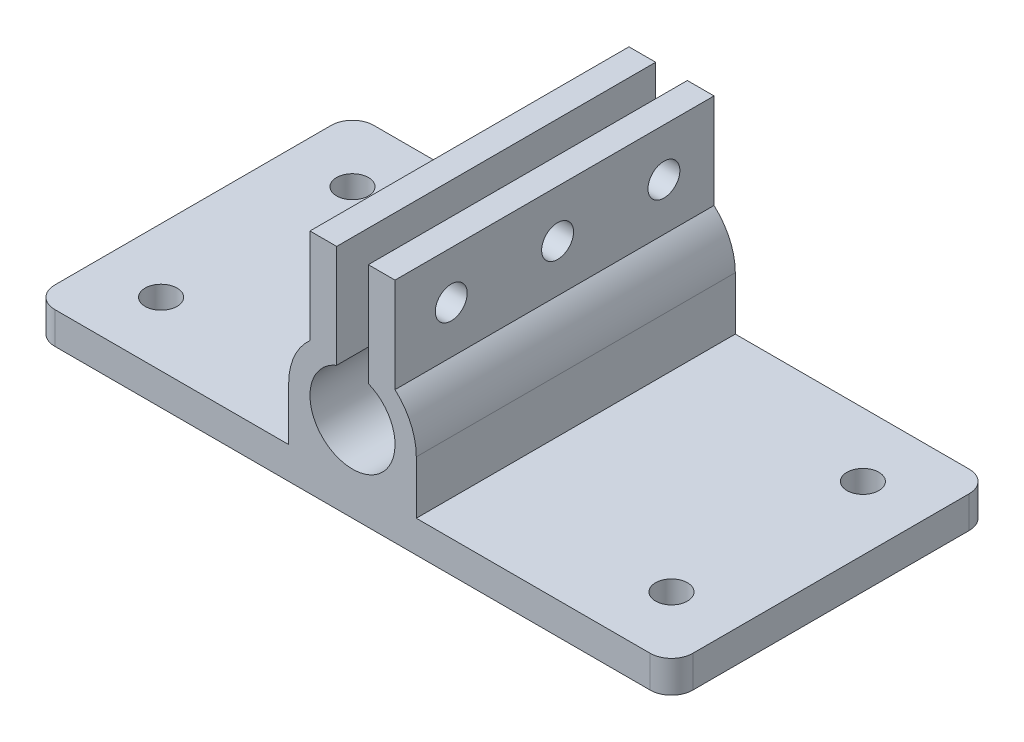
SolidWorks part; units mm, degrees
ref_plane "前视基准面" through (0, 0, 0) normal (0, 0, 1) x (1, 0, 0)
ref_plane "上视基准面" through (0, 0, 0) normal (0, 1, 0) x (1, 0, 0)
ref_plane "右视基准面" through (0, 0, 0) normal (1, 0, 0) x (0, 0, -1)
sketch "草图1" plane through (0, 0, 0) normal (0, 1, 0) x (1, 0, 0)
  line L1 (30, 15) -> (-30, 15)
  line L2 (30, 15) -> (30, -15)
  line L3 (30, -15) -> (-30, -15)
  line L4 (-30, 15) -> (-30, -15)
  line L5 (30, 15) -> (-30, -15) construction
  line L6 (30, -15) -> (-30, 15) construction
  point P0 (0, 0)
extrude "凸台-拉伸1" add sketch "草图1" along normal blind 3
sketch "草图2" plane through (0, 3, 0) normal (0, 1, 0) x (1, 0, 0)
  line L0 (-30, -9) -> (-24, -9) construction
  line L1 (-30, 15) -> (-30, -15) construction
  line L2 (-24, -9) -> (-24, -15) construction
  line L3 (-30, -15) -> (30, -15) construction
  circle A0 centre (-24, -9) radius 1.5
extrude "切除-拉伸1" cut sketch "草图2" against normal blind 3
mirror "镜向1" about plane through (0, 0, 0) normal (0, 0, 1) of "切除-拉伸1"
mirror "镜向2" about plane through (0, 0, 0) normal (1, 0, 0) of "镜向1", "切除-拉伸1"
fillet "圆角2" radius 2 4 edges at (-30, 1.5, -15) (30, 1.5, -15) (30, 1.5, 15) (-30, 1.5, 15)
sketch "草图5" plane through (0, 0, 15) normal (0, 0, 1) x (1, 0, 0)
  line L1 (-28, 3) -> (28, 3) construction
  circle A0 centre (0, 8) radius 6
  dimension "D1" = 5
extrude "凸台-拉伸2" add sketch "草图5" against normal up to surface (30 mm away) up to face at (0, 1.5, -15)
sketch "草图6" plane through (0, 0, 15) normal (0, 0, 1) x (1, 0, 0)
  line L0 (6, 8) -> (6, 3)
  line L1 (3.3166, 3) -> (28, 3) construction
  line L2 (6, 3) -> (-6, 3)
  line L3 (-28, 3) -> (-3.3166, 3) construction
  line L4 (-6, 3) -> (-6, 8)
  line L5 (-6, 8) -> (6, 8)
  arc A0 (3.3166, 3) -> (-3.3166, 3) centre (0, 8) ccw construction
extrude "凸台-拉伸3" add sketch "草图6" against normal up to surface (30 mm away) up to face at (0, 3.8333, -15)
sketch "草图7" plane through (0, 0, 15) normal (0, 0, 1) x (1, 0, 0)
  circle A0 centre (0, 8) radius 4
extrude "切除-拉伸4" cut sketch "草图7" against normal through all
sketch "草图8" plane through (0, 0, 15) normal (0, 0, 1) x (1, 0, 0)
  line L0 (0, 8) -> (0, 22.1886) construction
  line L2 (-4, 21.396) -> (4, 21.396)
  line L3 (-4, 21.396) -> (-4, 12.2415)
  line L4 (-4, 12.2415) -> (4, 12.2415)
  line L5 (4, 21.396) -> (4, 12.2415)
  line L6 (-4, 21.396) -> (4, 12.2415) construction
  line L7 (-4, 12.2415) -> (4, 21.396) construction
  point P4 (0, 16.8188)
  point P9 (0, 16.8188)
extrude "凸台-拉伸4" add sketch "草图8" against normal up to surface (30 mm away) up to face at (4, 8, -15)
sketch "草图9" plane through (0, 0, 15) normal (0, 0, 1) x (1, 0, 0)
  line L1 (-1.4884, 22.8266) -> (1.4884, 22.8266)
  line L2 (-1.4884, 22.8266) -> (-1.4884, 9.9673)
  line L3 (-1.4884, 9.9673) -> (1.4884, 9.9673)
  line L4 (1.4884, 22.8266) -> (1.4884, 9.9673)
  line L5 (-1.4884, 22.8266) -> (1.4884, 9.9673) construction
  line L6 (-1.4884, 9.9673) -> (1.4884, 22.8266) construction
  point P0 (0, 16.397)
extrude "切除-拉伸5" cut sketch "草图9" against normal through all
sketch "草图10" plane through (4, 0, 0) normal (1, 0, 0) x (0, 0, -1)
  line L0 (15, 16.9341) -> (-15, 16.9341) construction
  line L1 (15, 21.396) -> (15, 12.4721) construction
  line L2 (-15, 12.4721) -> (-15, 21.396) construction
  circle A0 centre (10.287, 16.9341) radius 1.5
  circle A1 centre (0.287, 16.9341) radius 1.5
  circle A2 centre (-9.713, 16.9341) radius 1.5
  dimension "D1" = 3
extrude "切除-拉伸6" cut sketch "草图10" against normal through all
